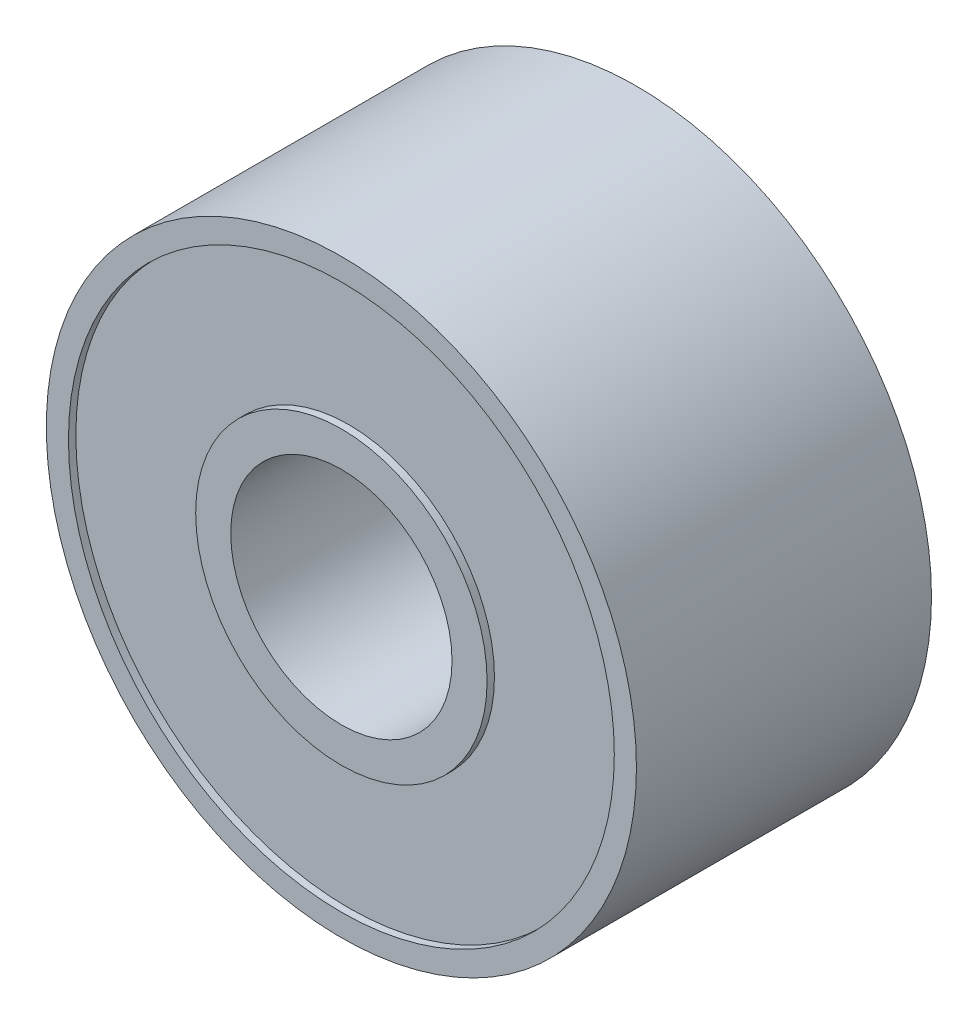
SolidWorks part; units mm, degrees
ref_plane "Front" through (0, 0, 0) normal (0, 0, 1) x (1, 0, 0)
ref_plane "Top" through (0, 0, 0) normal (0, 1, 0) x (1, 0, 0)
ref_plane "Right" through (0, 0, 0) normal (1, 0, 0) x (0, 0, -1)
sketch "Sketch1" plane through (0, 0, 0) normal (0, 0, 1) x (1, 0, 0)
  circle A0 centre (0, 0) radius 1.5
  circle A1 centre (0, 0) radius 4
  dimension "D1" = 3
  dimension "D2" = 8
extrude "Boss-Extrude1" add sketch "Sketch1" along normal blind 4
sketch "Sketch2" plane through (0, 0, 4) normal (0, 0, 1) x (1, 0, 0)
  circle A0 centre (0, 0) radius 1.9752
  circle A1 centre (0, 0) radius 3.7
  dimension "D1" = 7.4
extrude "Cut-Extrude1" cut sketch "Sketch2" against normal blind 0.1
sketch "Sketch3" plane through (0, 0, 0) normal (0, 0, -1) x (-1, 0, 0)
  circle A0 centre (0, 0) radius 1.9752 construction
  circle A1 centre (0, 0) radius 4
  circle A2 centre (0, 0) radius 4
  circle A3 centre (0, 0) radius 1.9752
  circle A4 centre (0, 0) radius 3.7 construction
  circle A5 centre (0, 0) radius 3.7
  dimension "D1" = 0
extrude "Cut-Extrude2" cut sketch "Sketch3" against normal blind 0.1 contours A5 A3
